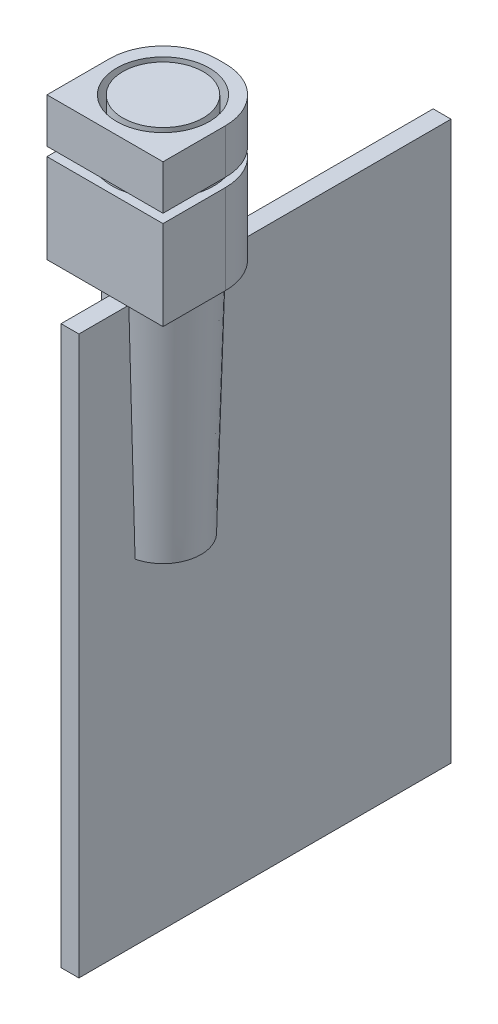
SolidWorks part; units mm, degrees
ref_plane "前视基准面" through (0, 0, 0) normal (0, 0, 1) x (1, 0, 0)
ref_plane "上视基准面" through (0, 0, 0) normal (0, 1, 0) x (1, 0, 0)
ref_plane "右视基准面" through (0, 0, 0) normal (1, 0, 0) x (0, 0, -1)
other "Configuration Table"
sketch "草图8" plane through (0, 0, 0) normal (0, 1, 0) x (1, 0, 0)
  circle A0 centre (0, 0) radius 450
  dimension "D1" = 900
extrude "凸台-拉伸3" add sketch "草图8" against normal blind 500
sketch "草图9" [suppressed] plane through (0, 0, 0) normal (0, 1, 0) x (1, 0, 0)
  line L0 (-1, -2) -> (-1, 2)
  line L1 (-1, -2) -> (1, -2)
  line L2 (-1, 2) -> (1, 2)
  line L3 (1, -2) -> (1, 2)
  line L4 (-1, -2) -> (1, 2) construction
  line L5 (-1, 2) -> (1, -2) construction
  line L6 (0, 2) -> (0, -2) construction
  point P1 (0, 0)
  dimension "D1" = 4
  dimension "D2" = 2
extrude "凸台-拉伸4" [suppressed] add sketch "草图9" against normal blind 0.2
sketch "草图19" plane through (0, 0, 0) normal (1, 0, 0) x (0, 0, -1)
  line L0 (450, -500) -> (500, -600)
  line L1 (500, -600) -> (500, -1500)
  line L2 (500, -1500) -> (0, -1500)
  line L3 (0, -1500) -> (0, -500)
  line L4 (-450, -500) -> (450, -500) construction
  line L5 (0, -500) -> (450, -500)
  dimension "D1" = 100
  dimension "D2" = 1000
  dimension "D3" = 500
revolve "旋转1" add sketch "草图19" angle 360 about L3
ref_plane "基准面4" through (0, -4250, 0) normal (0, -1, 0) x (-1, 0, 0)
sketch "草图20" plane through (0, -4250, 0) normal (0, -1, 0) x (-1, 0, 0)
  circle A0 centre (0, 0) radius 425
  dimension "D1" = 850
sketch "草图21" plane through (0, 0, 0) normal (1, 0, 0) x (0, 0, -1)
  line L0 (-425, -4250) -> (425, -4250) construction
  line L1 (-500, -1500) -> (500, -1500) construction
  line L2 (-425, -4250) -> (425, -4250)
  line L3 (-500, -1500) -> (500, -1500)
  line L4 (-425, -4250) -> (-500, -1500)
loft "放样2" add profiles "草图20" section edge at (0, -1500, -500) section "草图20"
sketch "草图22" plane through (0, 0, 0) normal (1, 0, 0) x (0, 0, -1)
  line L0 (500, -1500) -> (-500, -1500) construction
  line L1 (-1042.5, -1750) -> (3127.5, -1750)
  line L2 (-1042.5, -1750) -> (-1042.5, -8000)
  line L3 (-1042.5, -8000) -> (3127.5, -8000)
  line L4 (3127.5, -1750) -> (3127.5, -8000)
  line L5 (0, -1500) -> (0, -4250) construction
  dimension "D1" = 250
  dimension "D2" = 6250
  dimension "D3" = 4170
  dimension "D4" = 1042.5
extrude "凸台-拉伸9" add sketch "草图22" along normal mid plane 200
sketch "草图23" plane through (0, 0, 0) normal (0, 1, 0) x (1, 0, 0)
  line L1 (-650, 650) -> (650, 650)
  line L2 (-650, 650) -> (-650, -650)
  line L3 (-650, -650) -> (650, -650)
  line L4 (650, 650) -> (650, -650)
  line L5 (-650, 650) -> (650, -650) construction
  line L6 (-650, -650) -> (650, 650) construction
  circle A0 centre (0, 0) radius 520
  circle A1 centre (0, 0) radius 450 construction
  dimension "D3" = 70
  dimension "D1" = 1300
  dimension "D2" = 1300
extrude "凸台-拉伸10" add sketch "草图23" against normal blind 500 separate body
ref_plane "基准面5" through (0, -600, 0) normal (0, 1, 0) x (1, 0, 0)
sketch "草图24" plane through (0, -600, 0) normal (0, 1, 0) x (1, 0, 0)
  line L1 (650, -650) -> (-650, -650)
  line L2 (650, -650) -> (650, 650)
  line L3 (650, 650) -> (-650, 650)
  line L4 (-650, -650) -> (-650, 650)
  line L5 (650, -650) -> (-650, 650) construction
  line L6 (650, 650) -> (-650, -650) construction
  circle A0 centre (0, 0) radius 570
  circle A1 centre (0, 0) radius 500 construction
  dimension "D1" = 70
  dimension "D2" = 1300
  dimension "D3" = 1300
extrude "凸台-拉伸11" add sketch "草图24" against normal blind 1000 separate body
fillet "圆角1" radius 600 2 edges at (-650, -250, -650) (650, -250, -650)
fillet "圆角2" radius 600 2 edges at (-650, -1100, -650) (650, -1100, -650)
